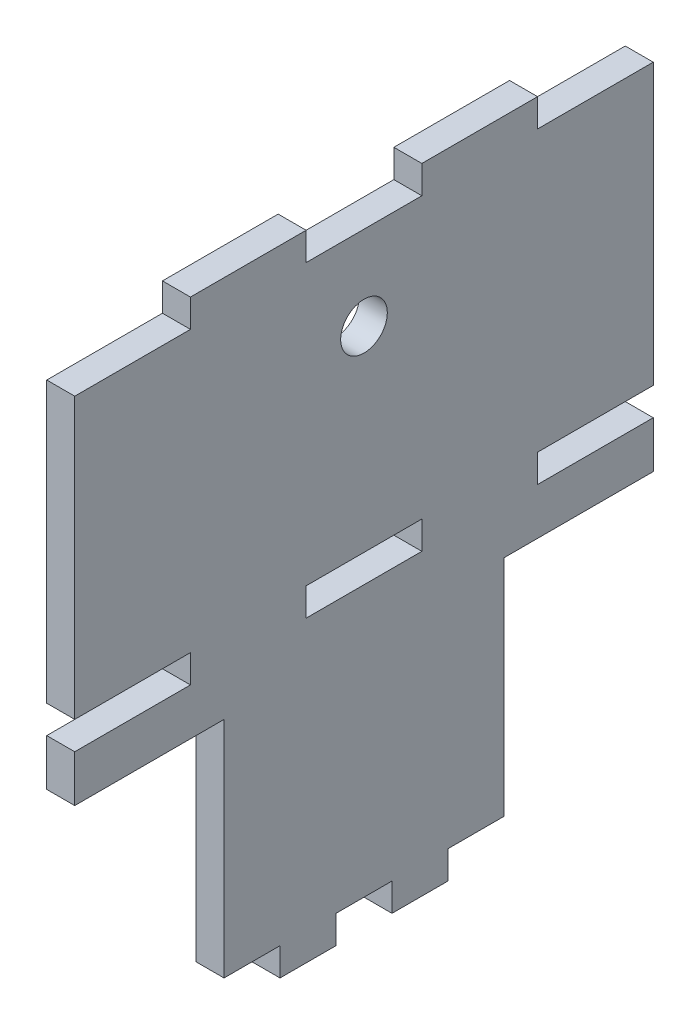
SolidWorks part; units mm, degrees
ref_plane "Ön Düzlem" through (0, 0, 0) normal (0, 0, 1) x (1, 0, 0)
ref_plane "Üst Düzlem" through (0, 0, 0) normal (0, 1, 0) x (1, 0, 0)
ref_plane "Sağ Düzlem" through (0, 0, 0) normal (1, 0, 0) x (0, 0, -1)
sketch "Sketch1" plane through (0, 0, 0) normal (1, 0, 0) x (0, 0, -1)
  line L0 (-9, -34) -> (-3, -34)
  line L1 (9, -34) -> (3, -34)
  line L2 (15, -31) -> (15, -7)
  line L4 (-15, -31) -> (-15, -7)
  line L5 (-6.2, 1) -> (-6.2, -2)
  line L7 (-9, -34) -> (-9, -31)
  line L9 (-3, -31) -> (-3, -34)
  line L11 (-3, -34) -> (-9, -34)
  line L12 (-9, -31) -> (-15, -31)
  line L14 (3, -34) -> (3, -31)
  line L15 (3, -31) -> (-3, -31)
  line L16 (-31, -7) -> (-31, -2)
  line L17 (9, -31) -> (9, -34)
  line L18 (9, -31) -> (15, -31)
  line L20 (18.6, 34) -> (6.2, 34)
  line L21 (-6.2, 34) -> (-18.6, 34)
  line L22 (31, 31) -> (31, 1)
  line L23 (-18.6, 34) -> (-6.2, 34)
  line L25 (6.2, 34) -> (18.6, 34)
  line L26 (-31, -7) -> (-15, -7)
  line L28 (-18.6, 34) -> (-18.6, 31)
  line L30 (15, -7) -> (31, -7)
  line L31 (-18.6, 31) -> (-31, 31)
  line L32 (-6.2, 34) -> (-6.2, 31)
  line L33 (6.2, 34) -> (6.2, 31)
  line L34 (18.6, 34) -> (18.6, 31)
  line L35 (6.2, 31) -> (-6.2, 31)
  line L36 (18.6, 31) -> (31, 31)
  line L37 (-18.6, 1) -> (-31, 1)
  line L38 (-18.6, 1) -> (-18.6, -2)
  line L39 (-18.6, -2) -> (-31, -2)
  line L40 (18.6, -2) -> (31, -2)
  line L41 (-31, 1) -> (-31, 31)
  line L42 (18.6, 1) -> (18.6, -2)
  line L43 (18.6, 1) -> (31, 1)
  line L44 (31, -2) -> (31, -7)
  line L45 (6.2, 1) -> (6.2, -2)
  line L46 (6.2, -2) -> (-6.2, -2)
  line L47 (6.2, 1) -> (-6.2, 1)
  circle A0 centre (0, 22) radius 2.5
  point P0 (0, 0)
extrude "Boss-Extrude3" add sketch "Sketch1" along normal blind 3 contours L44 L40 L42 L43 L22 L36 L34 L20 L33 L35 L32 L21 L28 L31 L41 L37 L38 L39 L16 L26 L4 L12 L7 L0 L9 L15 L14 L1 L17 L18 L2 L30 A0 L47 L45 L46 L5
